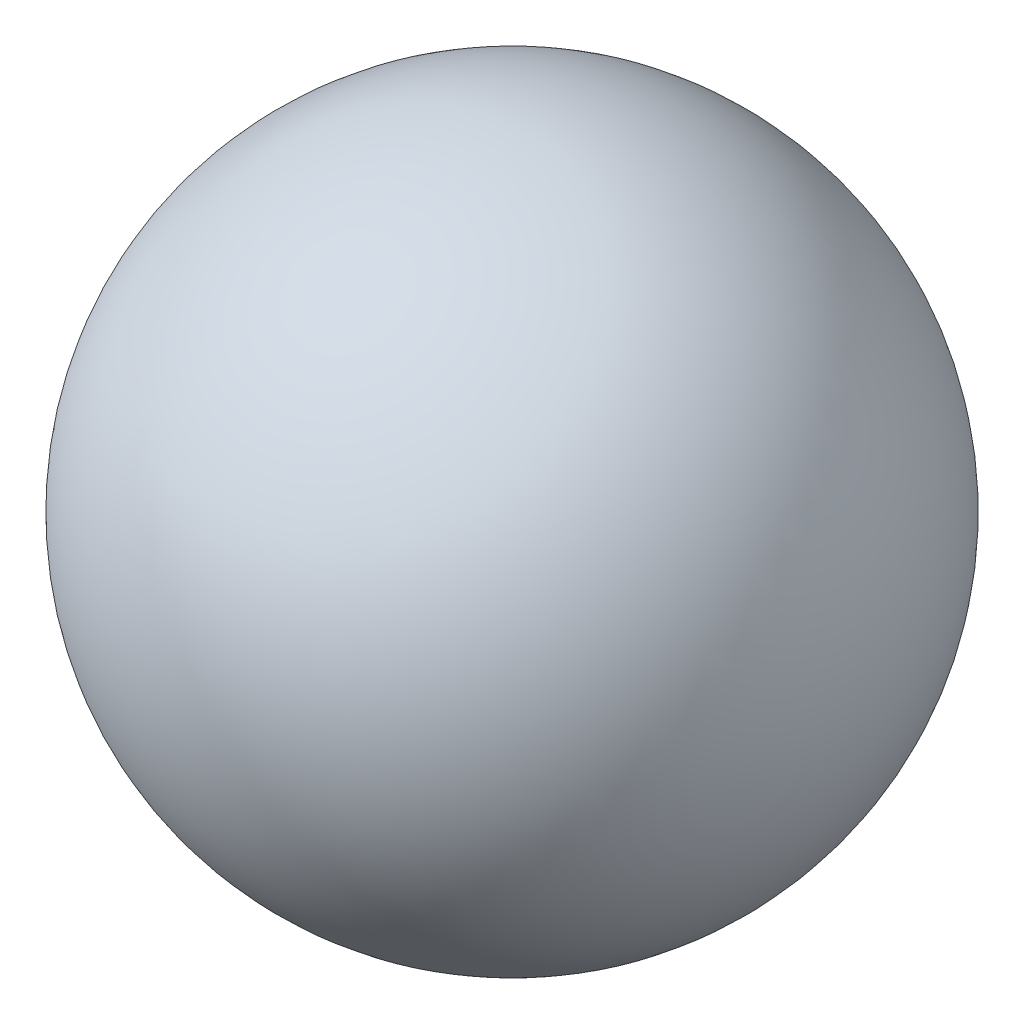
SolidWorks part; units mm, degrees
material "Stainless Steel (ferritic)"
ref_plane "Front Plane" through (0, 0, 0) normal (0, 0, 1) x (1, 0, 0)
ref_plane "Top Plane" through (0, 0, 0) normal (0, 1, 0) x (1, 0, 0)
ref_plane "Right Plane" through (0, 0, 0) normal (1, 0, 0) x (0, 0, -1)
sketch "Sketch1" plane through (0, 0, 0) normal (0, 0, 1) x (1, 0, 0)
  line L0 (0, 1) -> (0, -1)
  arc A0 (0, 1) -> (0, -1) centre (0, 0) ccw
revolve "Revolve1" add sketch "Sketch1" angle 360 about L0
